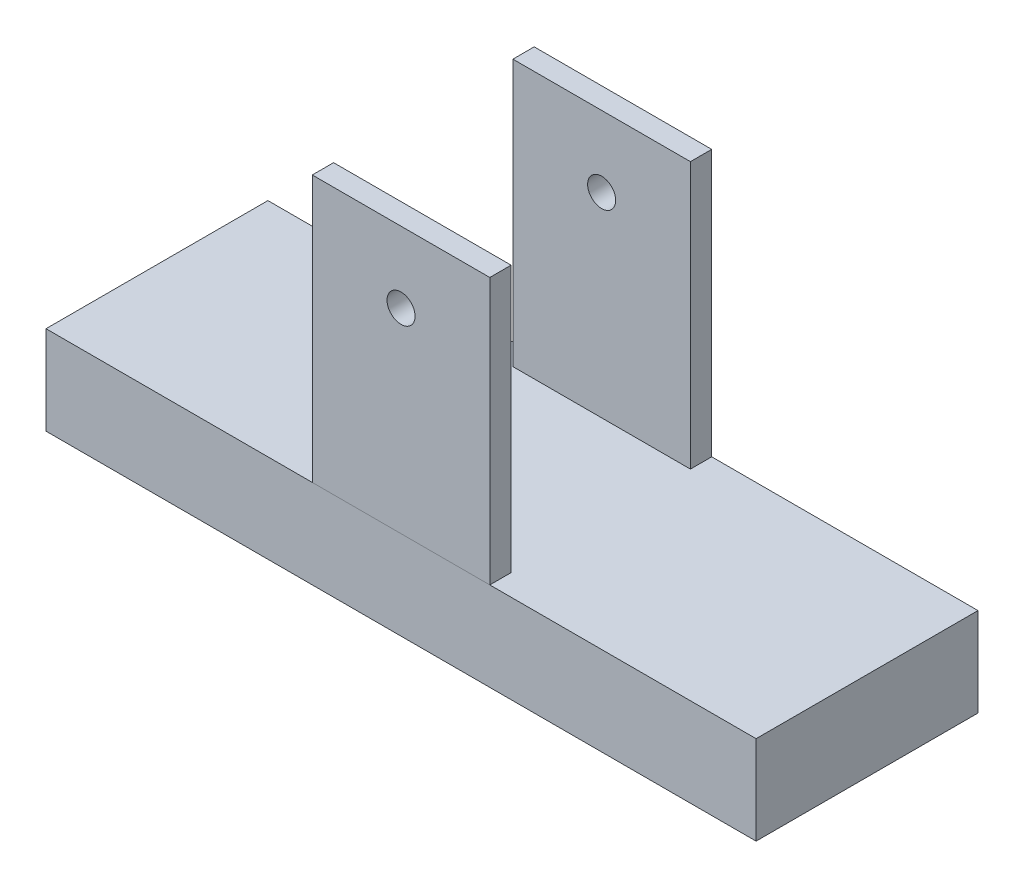
SolidWorks part; units mm, degrees
material "Pine"
ref_plane "Front Plane" through (0, 0, 0) normal (0, 0, 1) x (1, 0, 0)
ref_plane "Top Plane" through (0, 0, 0) normal (0, 1, 0) x (1, 0, 0)
ref_plane "Right Plane" through (0, 0, 0) normal (1, 0, 0) x (0, 0, -1)
sketch "Sketch1" plane through (0, 0, 0) normal (0, 0, 1) x (1, 0, 0)
  line L1 (0, 0) -> (-400, 0)
  line L2 (0, 0) -> (0, 50)
  line L3 (0, 50) -> (-400, 50)
  line L4 (-400, 0) -> (-400, 50)
  dimension "D1" = 50
  dimension "D2" = 400
extrude "Boss-Extrude1" add sketch "Sketch1" against normal blind 125
sketch "Sketch2" plane through (0, 50, 0) normal (0, 1, 0) x (1, 0, 0)
  line L0 (-400, 0) -> (-250, 0) construction
  line L1 (0, 0) -> (-400, 0) construction
  line L2 (-250, 0) -> (-250, 12)
  line L3 (-250, 12) -> (-150, 12)
  line L4 (-150, 12) -> (-150, 0)
  line L5 (-150, 0) -> (-250, 0)
  line L6 (-400, 125) -> (-400, 0) construction
  line L7 (-400, 62.5) -> (0, 62.5) construction
  line L8 (0, 125) -> (0, 0) construction
  line L9 (-150, 113) -> (-150, 125)
  line L10 (-150, 125) -> (-250, 125)
  line L11 (-250, 125) -> (-250, 113)
  line L12 (-250, 113) -> (-150, 113)
  dimension "D1" = 150
  dimension "D2" = 100
  dimension "D3" = 12
extrude "Boss-Extrude2" add sketch "Sketch2" along normal blind 150 separate body
sketch "Sketch3" plane through (0, 0, 0) normal (0, 0, 1) x (1, 0, 0)
  line L0 (-200, 200) -> (-200, 160) construction
  line L1 (-250, 200) -> (-150, 200) construction
  circle A0 centre (-200, 160) radius 7.9
  dimension "D1" = 15.8
  dimension "D2" = 40
extrude "Cut-Extrude1" cut sketch "Sketch3" against normal through all both and the other way through all
